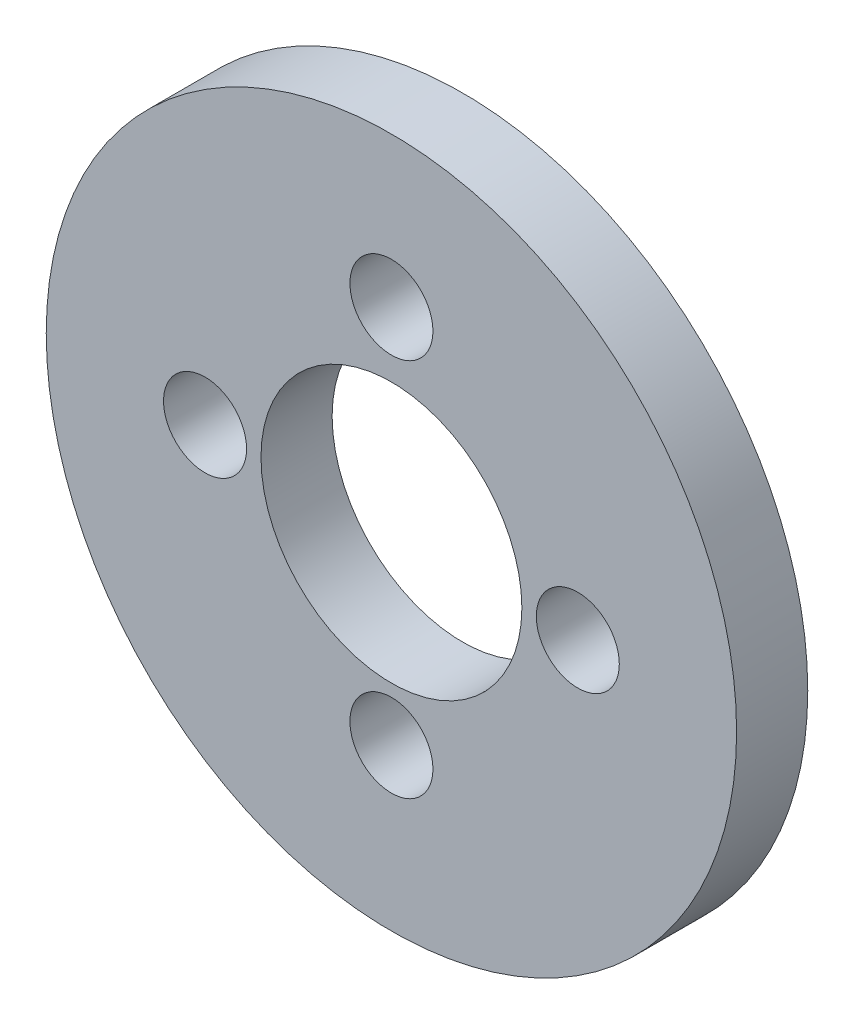
SolidWorks part; units mm, degrees
ref_plane "Front Plane" through (0, 0, 0) normal (0, 0, 1) x (1, 0, 0)
ref_plane "Top Plane" through (0, 0, 0) normal (0, 1, 0) x (1, 0, 0)
ref_plane "Right Plane" through (0, 0, 0) normal (1, 0, 0) x (0, 0, -1)
sketch "Sketch1" plane through (0, 0, 0) normal (0, 0, 1) x (1, 0, 0)
  circle A0 centre (0, 0) radius 6
  circle A1 centre (0, 0) radius 10.0192
  circle A2 centre (0, 0) radius 14.5546
  circle A3 centre (0, 8.2281) radius 1.75
  circle A4 centre (-7.8583, 0) radius 1.75
  circle A5 centre (0, -7.7658) radius 1.75
  circle A6 centre (7.8583, 0) radius 1.75
  dimension "D1" = 12
  dimension "D2" = 3.5
  dimension "D3" = 3.5
  dimension "D4" = 3.5
  dimension "D5" = 3.5
extrude "Boss-Extrude1" add sketch "Sketch1" along normal blind 3 contours A1 A6 A5 A4 A3 A0 | A2 A1
sketch "Sketch2" plane through (0, 0, 3) normal (0, 0, 1) x (1, 0, 0)
  circle A0 centre (0, 0) radius 5.5
  dimension "D1" = 11
extrude "Cut-Extrude1" cut sketch "Sketch2" against normal blind 3
